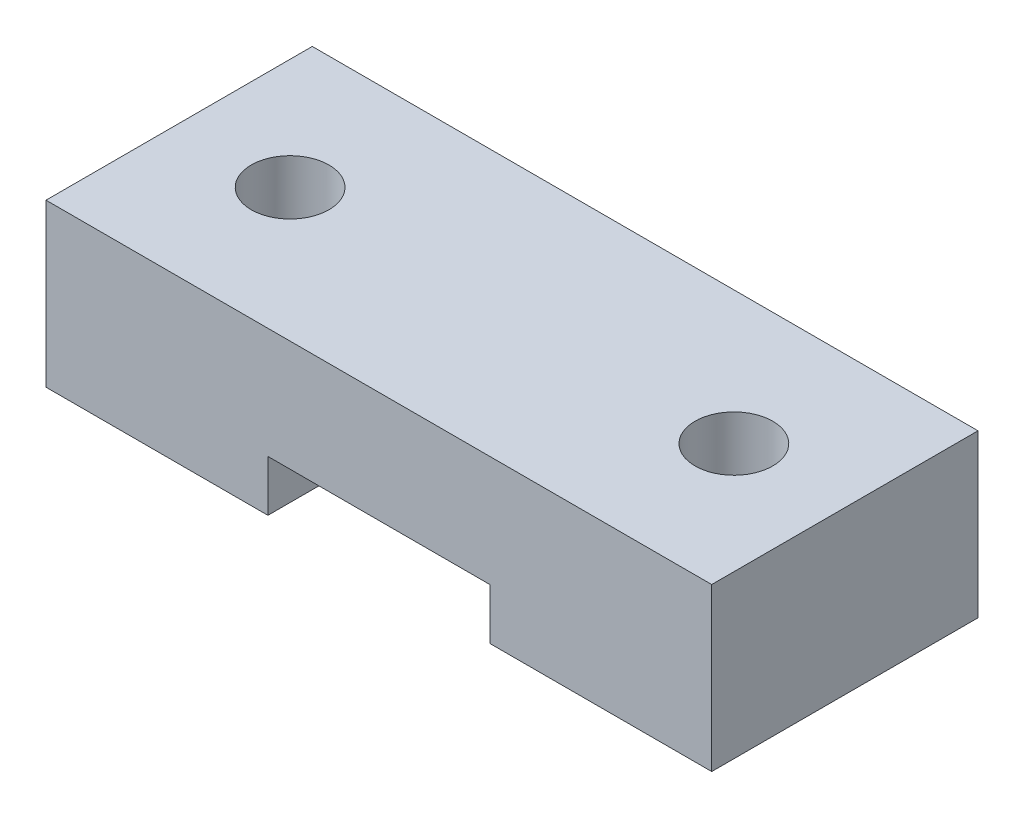
SolidWorks part; units mm, degrees
ref_plane "正面(Front)" through (0, 0, 0) normal (0, 0, 1) x (1, 0, 0)
ref_plane "平面(Top)" through (0, 0, 0) normal (0, 1, 0) x (1, 0, 0)
ref_plane "右側面(Right)" through (0, 0, 0) normal (1, 0, 0) x (0, 0, -1)
sketch "ｽｹｯﾁ1" plane through (0, 0, 0) normal (0, 0, 1) x (1, 0, 0)
  line L1 (0, 0) -> (30, 0)
  line L2 (0, 0) -> (0, 61.5)
  line L3 (0, 61.5) -> (30, 61.5)
  line L4 (30, 0) -> (30, 61.5)
  dimension "D1" = 30
  dimension "D2" = 61.5
extrude "ﾎﾞｽ - 押し出し1" add sketch "ｽｹｯﾁ1" along normal blind 5
sketch "ｽｹｯﾁ2" plane through (0, 0, 5) normal (0, 0, 1) x (1, 0, 0)
  line L0 (15, 0) -> (15, 69.5246) construction
  line L1 (0, 0) -> (30, 0) construction
  line L2 (15, 28.2) -> (37.391, 28.2) construction
  line L3 (4.5, 48.7) -> (25.5, 48.7)
  line L4 (4.5, 48.7) -> (4.5, 7.7)
  line L5 (4.5, 7.7) -> (25.5, 7.7)
  line L6 (25.5, 48.7) -> (25.5, 7.7)
  line L7 (4.5, 48.7) -> (25.5, 7.7) construction
  line L8 (4.5, 7.7) -> (25.5, 48.7) construction
  line L9 (15, 18.2) -> (37.9351, 18.2) construction
  circle A0 centre (10, 3.5) radius 1.75
  circle A1 centre (20, 3.5) radius 1.75
  circle A2 centre (10, 53) radius 1.75
  circle A3 centre (20, 53) radius 1.75
  point P4 (15, 28.2)
  dimension "D1" = 5
  dimension "D3" = 14.7
  dimension "D5" = 3.5
  dimension "D7" = 3.5
  dimension "D9" = 10
  dimension "D2" = 41
  dimension "D4" = 10
  dimension "D6" = 21
  dimension "D8" = 34.8
extrude "ｶｯﾄ - 押し出し1" cut sketch "ｽｹｯﾁ2" against normal through all
sketch "ｽｹｯﾁ3" plane through (0, 61.5, 0) normal (0, 1, 0) x (1, 0, 0)
  line L0 (30, -5) -> (30, 0) construction
  line L1 (0, 0) -> (30, 0)
  line L2 (0, 0) -> (0, 40)
  line L3 (0, 40) -> (30, 40)
  line L4 (30, 0) -> (30, 40)
  dimension "D1" = 40
extrude "ﾎﾞｽ - 押し出し2" add sketch "ｽｹｯﾁ3" against normal blind 5
sketch "ｽｹｯﾁ4" plane through (0, 61.5, 0) normal (0, 1, 0) x (1, 0, 0)
  line L0 (0, 25) -> (30, 25) construction
  line L1 (0, -5) -> (0, 40) construction
  line L2 (30, -5) -> (30, 40) construction
  line L3 (15, -5) -> (15, 47.6868) construction
  line L4 (30, -5) -> (0, -5) construction
  line L5 (30, 40) -> (0, 40) construction
  circle A0 centre (5, 25) radius 1.75
  circle A1 centre (25, 25) radius 1.75
  dimension "D1" = 3.5
  dimension "D2" = 20
  dimension "D3" = 15
extrude "ｶｯﾄ - 押し出し2" cut sketch "ｽｹｯﾁ4" against normal through all
sketch "ｽｹｯﾁ5" plane through (0, 56.5, 0) normal (0, -1, 0) x (1, 0, 0)
  line L0 (15, 0) -> (15, -30.8801) construction
  line L1 (5, -28.6) -> (8.1177, -26.8)
  line L2 (8.1177, -26.8) -> (8.1177, -23.2)
  line L3 (8.1177, -23.2) -> (5, -21.4)
  line L4 (5, -21.4) -> (1.8823, -23.2)
  line L5 (1.8823, -23.2) -> (1.8823, -26.8)
  line L6 (1.8823, -26.8) -> (5, -28.6)
  line L7 (0, 0) -> (30, 0) construction
  line L8 (28.1177, -26.8) -> (25, -28.6)
  line L9 (28.1177, -23.2) -> (28.1177, -26.8)
  line L10 (25, -21.4) -> (28.1177, -23.2)
  line L11 (21.8823, -23.2) -> (25, -21.4)
  line L12 (21.8823, -26.8) -> (21.8823, -23.2)
  line L13 (25, -28.6) -> (21.8823, -26.8)
  line L14 (0, -40) -> (0, 0) construction
  line L15 (10, -19) -> (0, -19)
  line L16 (10, -19) -> (10, -31)
  line L17 (10, -31) -> (0, -31)
  line L18 (0, -19) -> (0, -31)
  line L19 (10, -19) -> (0, -31) construction
  line L20 (10, -31) -> (0, -19) construction
  line L21 (20, -31) -> (30, -31)
  line L22 (30, -19) -> (30, -31)
  line L23 (20, -19) -> (30, -19)
  line L24 (20, -19) -> (20, -31)
  circle A0 centre (5, -25) radius 3.1177 construction
  dimension "D1" = 7.2
  dimension "D2" = 12
extrude "ﾎﾞｽ - 押し出し3" add sketch "ｽｹｯﾁ5" along normal blind 2.3
sketch "ｽｹｯﾁ6" plane through (0, 61.5, 0) normal (0, 1, 0) x (1, 0, 0)
  line L0 (30, -5) -> (30, 40) construction
  line L1 (0, -5) -> (30, -5)
  line L2 (0, -5) -> (0, 7)
  line L3 (0, 7) -> (30, 7)
  line L4 (30, -5) -> (30, 7)
  dimension "D1" = 12
extrude "ﾎﾞｽ - 押し出し4" add sketch "ｽｹｯﾁ6" along normal blind 4
sketch "ｽｹｯﾁ7" plane through (30, 0, 0) normal (1, 0, 0) x (0, 0, -1)
  line L0 (40, 56.5) -> (40, 39.5)
  line L1 (40, 39.5) -> (0, 9.8226)
  line L2 (0, 0) -> (0, 56.5) construction
  line L3 (0, 9.8226) -> (0, 21.5)
  line L4 (0, 21.5) -> (31, 44.5)
  line L5 (31, 44.5) -> (31, 56.5)
  line L6 (31, 56.5) -> (40, 56.5)
  line L7 (0, 56.5) -> (19, 56.5) construction
  dimension "D1" = 17
  dimension "D2" = 12
  dimension "D3" = 35
extrude "ﾎﾞｽ - 押し出し5" add sketch "ｽｹｯﾁ7" against normal blind 4.5
ref_plane "平面1" through (15, 0, 0) normal (-1, 0, 0) x (0, 0, 1)
mirror "ﾐﾗｰ1" about plane through (15, 0, 0) normal (-1, 0, 0) of "ﾎﾞｽ - 押し出し5"
fillet "ﾌｨﾚｯﾄ1" radius 5 2 edges at (0, 0, 2.5) (30, 0, 2.5)
sketch "ｽｹｯﾁ8" plane through (0, 56.5, 0) normal (0, -1, 0) x (1, 0, 0)
  line L0 (25.5, -40) -> (25.5, -31) construction
  line L1 (4.5, -40) -> (25.5, -40)
  line L2 (4.5, -40) -> (4.5, -34)
  line L3 (4.5, -34) -> (25.5, -34)
  line L4 (25.5, -40) -> (25.5, -34)
  dimension "D1" = 6
extrude "ｶｯﾄ - 押し出し3" cut sketch "ｽｹｯﾁ8" against normal through all
sketch "ｽｹｯﾁ9" plane through (0, 0, 0) normal (-1, 0, 0) x (0, 0, 1)
  line L0 (-7, 61.5) -> (-40, 61.5) construction
  line L1 (-19, 54.2) -> (-31, 54.2)
  line L2 (-19, 54.2) -> (-19, 61.5)
  line L3 (-19, 61.5) -> (-31, 61.5)
  line L4 (-31, 54.2) -> (-31, 61.5)
  line L5 (-31, 54.2) -> (-31, 44.5) construction
extrude "ｶｯﾄ - 押し出し4" cut sketch "ｽｹｯﾁ9" against normal through all flip side to cut
